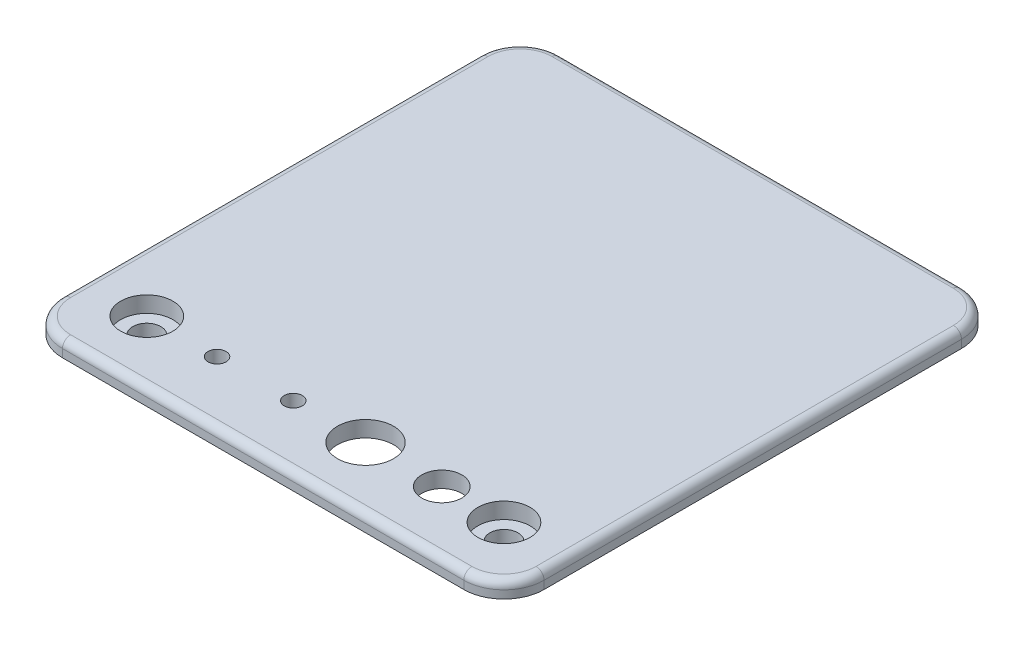
SolidWorks part; units mm, degrees
ref_plane "Front Plane" through (0, 0, 0) normal (0, 0, 1) x (1, 0, 0)
ref_plane "Top Plane" through (0, 0, 0) normal (0, 1, 0) x (1, 0, 0)
ref_plane "Right Plane" through (0, 0, 0) normal (1, 0, 0) x (0, 0, -1)
sketch "Sketch1" plane through (0, 0, 0) normal (0, 1, 0) x (1, 0, 0)
  line L1 (25, -31) -> (-25, -31)
  line L2 (30, -26) -> (30, 26)
  line L3 (25, 31) -> (-25, 31)
  line L4 (-30, -26) -> (-30, 26)
  line L5 (30, -31) -> (-30, 31) construction
  line L6 (30, 31) -> (-30, -31) construction
  arc A0 (25, -31) -> (30, -26) centre (25, -26) ccw
  arc A1 (-30, -26) -> (-25, -31) centre (-25, -26) ccw
  arc A2 (30, 26) -> (25, 31) centre (25, 26) ccw
  arc A3 (-30, 26) -> (-25, 31) centre (-25, 26) cw
  circle A4 centre (-13.5, -23.25) radius 1.125
  circle A5 centre (-4, -23.25) radius 1.125
  circle A6 centre (14.5, -23.25) radius 2.5
  circle A7 centre (5, -23.25) radius 3.5
  point P0 (0, 0)
  dimension "D3" = 5
  dimension "D4" = 5
  dimension "D5" = 7
  dimension "D6" = 2.25
  dimension "D7" = 2.25
  dimension "D1" = 62
  dimension "D2" = 60
  dimension "D8" = 9.5
  dimension "D9" = 9
  dimension "D10" = 9.5
  dimension "D11" = 7.75
  dimension "D12" = 15.5
extrude "Boss-Extrude1" add sketch "Sketch1" along normal blind 2
sketch "Sketch2" plane through (0, 0, 0) normal (0, -1, 0) x (1, 0, 0)
  line L4 (25, 31) -> (-25, 31)
  line L5 (-30, 26) -> (-30, -26)
  line L6 (-25, -31) -> (25, -31)
  line L7 (30, -26) -> (30, 26)
  line L8 (25, 31) -> (-25, 31)
  line L9 (-30, 26) -> (-30, -26)
  line L10 (-25, -31) -> (25, -31)
  line L11 (30, -26) -> (30, 26)
  circle A0 centre (-22.25, 23.25) radius 4
  circle A1 centre (22.25, 23.25) radius 4
  circle A2 centre (14.5, 23.25) radius 2.5 construction
  circle A3 centre (5, 23.25) radius 3.5 construction
  arc A4 (30, 26) -> (25, 31) centre (25, 26) ccw
  arc A5 (-25, 31) -> (-30, 26) centre (-25, 26) ccw
  arc A6 (-30, -26) -> (-25, -31) centre (-25, -26) ccw
  arc A7 (25, -31) -> (30, -26) centre (25, -26) ccw
  arc A8 (30, 26) -> (25, 31) centre (25, 26) ccw
  arc A9 (-25, 31) -> (-30, 26) centre (-25, 26) ccw
  arc A10 (-30, -26) -> (-25, -31) centre (-25, -26) ccw
  arc A11 (25, -31) -> (30, -26) centre (25, -26) ccw
  circle A12 centre (-13.5, 23.25) radius 1.125 construction
  circle A13 centre (-4, 23.25) radius 1.125 construction
  circle A14 centre (14.5, 23.25) radius 2.5
  circle A15 centre (5, 23.25) radius 3.5
  circle A16 centre (-13.5, 23.25) radius 1.125
  circle A17 centre (-4, 23.25) radius 1.125
  dimension "D2" = 8
  dimension "D3" = 7.75
  dimension "D4" = 7.75
  dimension "D1" = 0
extrude "Boss-Extrude2" add sketch "Sketch2" along normal blind 2 contours A0 | A1
sketch "Sketch3" plane through (0, -2, 0) normal (0, -1, 0) x (1, 0, 0)
  circle A1 centre (-22.25, 23.25) radius 4
  circle A2 centre (-22.25, 23.25) radius 4
  circle A3 centre (-22.25, 23.25) radius 1.75
  circle A4 centre (22.25, 23.25) radius 4
  circle A5 centre (22.25, 23.25) radius 4
  circle A6 centre (22.25, 23.25) radius 1.75
  dimension "D3" = 3.5
  dimension "D1" = 0
  dimension "D2" = 0
extrude "Cut-Extrude1" cut sketch "Sketch3" against normal through all contours A3 | A6
sketch "Sketch4" plane through (0, 2, 0) normal (0, 1, 0) x (1, 0, 0)
  line L4 (30, -26) -> (30, 26)
  line L5 (25, 31) -> (-25, 31)
  line L6 (-30, 26) -> (-30, -26)
  line L7 (-25, -31) -> (25, -31)
  line L8 (30, -26) -> (30, 26)
  line L9 (25, 31) -> (-25, 31)
  line L10 (-30, 26) -> (-30, -26)
  line L11 (-25, -31) -> (25, -31)
  circle A0 centre (-22.25, -23.25) radius 1.75 construction
  circle A1 centre (-22.25, -23.25) radius 1.75
  circle A2 centre (22.25, -23.25) radius 1.75 construction
  circle A3 centre (22.25, -23.25) radius 1.75
  arc A4 (25, -31) -> (30, -26) centre (25, -26) ccw
  arc A5 (30, 26) -> (25, 31) centre (25, 26) ccw
  arc A6 (-25, 31) -> (-30, 26) centre (-25, 26) ccw
  arc A7 (-30, -26) -> (-25, -31) centre (-25, -26) ccw
  arc A8 (25, -31) -> (30, -26) centre (25, -26) ccw
  arc A9 (30, 26) -> (25, 31) centre (25, 26) ccw
  arc A10 (-25, 31) -> (-30, 26) centre (-25, 26) ccw
  arc A11 (-30, -26) -> (-25, -31) centre (-25, -26) ccw
  circle A12 centre (-22.25, -23.25) radius 3.25
  circle A13 centre (22.25, -23.25) radius 3.25
  circle M9 centre (-22.25, -23.25) radius 1.75
  circle M10 centre (22.25, -23.25) radius 1.75
  dimension "D2" = 6.5
  dimension "D1" = 0
extrude "Cut-Extrude2" cut sketch "Sketch4" against normal blind 2 contours A12 M9 | A13 M10
sketch "Sketch6" plane through (0, 0, 0) normal (0, -1, 0) x (1, 0, 0)
  line L0 (25, -31) -> (-25, -31) construction
  line L1 (-10, -29) -> (10, -29)
  line L2 (-10, -29) -> (-10, -26.25)
  line L3 (-10, -26.25) -> (10, -26.25)
  line L4 (10, -29) -> (10, -26.25)
  line L5 (-10, -29) -> (10, -26.25) construction
  line L6 (-10, -26.25) -> (10, -29) construction
  point P0 (0, -27.625)
  point P7 (0, -31)
  dimension "D1" = 20
  dimension "D2" = 2.75
  dimension "D3" = 2
extrude "Boss-Extrude3" add sketch "Sketch6" along normal blind 4
ref_plane "Plane1" through (8, 0, 0) normal (1, 0, 0) x (0, 0, -1)
sketch "Sketch7" plane through (8, 0, 0) normal (1, 0, 0) x (0, 0, -1)
  line L0 (29, -3) -> (27, 0)
  line L1 (29, -3) -> (29, 0)
  line L2 (29, 0) -> (27, 0)
  line L4 (29, 0) -> (26.25, 0)
  line L5 (26.25, 0) -> (26.25, -4)
  line L6 (26.25, -4) -> (29, -4)
  line L7 (29, -4) -> (29, 0)
  line L8 (29, 0) -> (26.25, 0)
  line L9 (26.25, 0) -> (26.25, -4)
  line L10 (26.25, -4) -> (29, -4)
  line L11 (29, -4) -> (29, 0)
  dimension "D2" = 2
  dimension "D3" = 3
  dimension "D1" = 0
extrude "Cut-Extrude3" cut sketch "Sketch7" against normal blind 16 contours L1 L0 L2
fillet "Fillet1" radius 2 2 edges at (-10, -4, -27.625) (10, -4, -27.625)
fillet "Fillet2" radius 1 8 edges at (-28.5355, 2, -29.5355) (0, 2, -31) (28.5355, 2, -29.5355) (30, 2, 0) (28.5355, 2, 29.5355) (0, 2, 31) (-28.5355, 2, 29.5355) (-30, 2, 0)
equation "\"D4@Sketch2\"=\"D3@Sketch2\""
